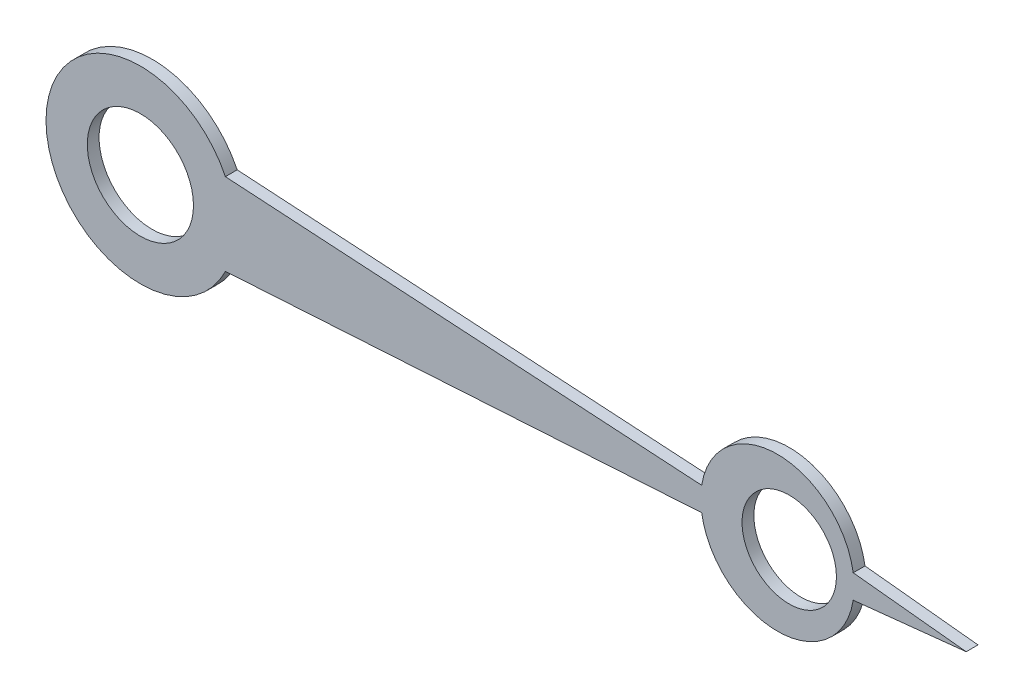
SolidWorks part; units mm, degrees
ref_plane "Front Plane" through (0, 0, 0) normal (0, 0, 1) x (1, 0, 0)
ref_plane "Top Plane" through (0, 0, 0) normal (0, 1, 0) x (1, 0, 0)
ref_plane "Right Plane" through (0, 0, 0) normal (1, 0, 0) x (0, 0, -1)
sketch "Sketch1" plane through (0, 0, 0) normal (0, 0, 1) x (1, 0, 0)
  line L0 (55, 0) -> (70, 0) construction
  line L1 (55, 0) -> (70, 0) construction
  line L2 (0, 0) -> (55, 0) construction
  line L3 (0, 0) -> (55, 0) construction
  line L4 (60.4216, 1.0067) -> (70, 0)
  line L5 (47.5784, 1.0067) -> (7.2053, 3.4761)
  line L6 (60.4216, -1.0067) -> (70, 0)
  line L7 (47.5784, -1.0067) -> (7.2053, -3.4761)
  arc A0 (7.2053, 3.4761) -> (7.2053, -3.4761) centre (0, 0) ccw
  circle A1 centre (55, 0) radius 4
  arc A2 (47.5784, -1.0067) -> (60.4216, -1.0067) centre (54, 0) ccw
  arc A3 (60.4216, 1.0067) -> (47.5784, 1.0067) centre (54, 0) ccw
  circle A4 centre (0, 0) radius 4.5 construction
  circle A5 centre (0, 0) radius 4.5
  dimension "D1" = 16
  dimension "D2" = 8
  dimension "D3" = 13
  dimension "D4" = 1
  dimension "D5" = 6
  dimension "D6" = 15
  dimension "D7" = 3.5
extrude "Boss-Extrude1" add sketch "Sketch1" along normal up to vertex (20 mm away) from vertex at 19
